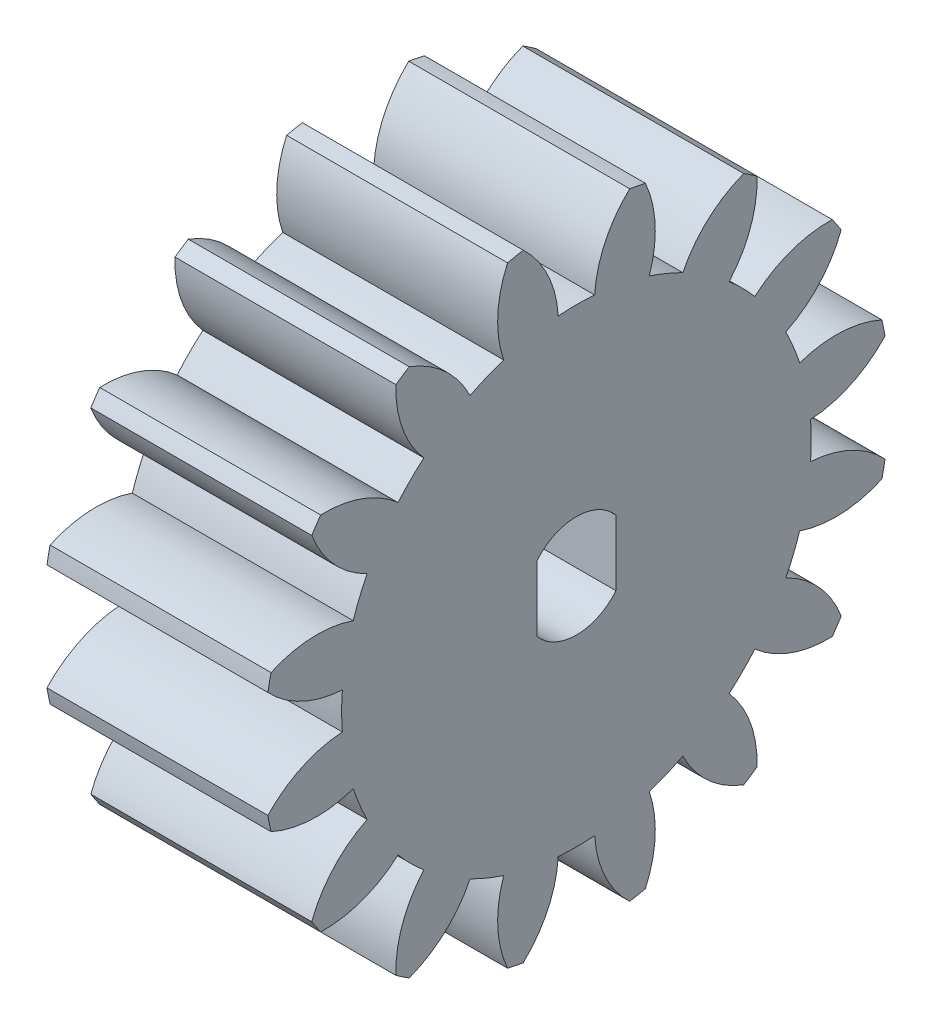
SolidWorks part; units mm, degrees
ref_plane "Plane1" through (0, 0, 0) normal (0, 0, 1) x (1, 0, 0)
ref_plane "Plane2" through (0, 0, 0) normal (0, 1, 0) x (1, 0, 0)
ref_plane "Plane3" through (0, 0, 0) normal (1, 0, 0) x (0, 0, -1)
sketch "HoldingSke" plane through (0, 0, 0) normal (0, 1, 0) x (1, 0, 0)
  line L0 (0, 0) -> (0.9613, -0.2756)
  line L1 (-15, 0) -> (100, 0) construction
  line L2 (0, 0) -> (-2.1039, 2.3779)
  line L3 (0, 0) -> (-11.863, 4.5341)
  line L4 (0, 0) -> (8.3015, 2.3804)
  line L5 (0, 0) -> (-46.8476, -17.4728)
  line L6 (0, 0) -> (-5.2639, -3.5516)
  line L7 (-2.1039, 2.3779) -> (8.6589, 51.2071)
  line L8 (-76.2, 54.61) -> (-76.1, 54.61)
  line L9 (-71.009, 38.7566) -> (-53.1078, 45.2721)
  line L10 (-76.2, 71.12) -> (104.1128, 71.12)
  line L11 (0, 0) -> (-6.35, 0)
  line L12 (-76.2, 101.6) -> (-76.162, 101.6)
  line L13 (24.9733, 27.94) -> (52.9518, 28.4284)
  line L14 (24.9733, 27.94) -> (24.9743, 27.94)
  line L15 (24.9733, 27.94) -> (100.4006, 29.5858)
  line L16 (-63.627, -1) -> (-12.827, -1)
  circle A0 centre (0, 0) radius 0.5
  circle A1 centre (0, 0) radius 6.749
  circle A2 centre (0, 0) radius 37.5
  circle A3 centre (0, 0) radius 0.5
  dimension "MHD" = 13.498
  dimension "Hub_dia" = 75
  dimension "Bore" = 1
  dimension "MBD" = 1
  dimension "Num_teeth" = 16
  dimension "Pitch_radius" = 180.3128
  dimension "Pitch" = 1
  dimension "Width" = 6.35
  dimension "Overall_len" = 50
  dimension "Show_teeth" = 16
  dimension "Thickness" = 6.35
  dimension "OAL" = 50.0013
  dimension "T_dim" = 0.1
  dimension "Ap" = 20
  dimension "H" = 19.05
  dimension "Backlash" = 0.038
  dimension "Addendum_fac" = 1
  dimension "Dedendum_fac" = 1.25
  dimension "Clearance_fac" = 0.25
  dimension "Dedendum_add" = 0.001
  dimension "Module" = 1
sketch "BasProSke" plane through (0, 0, 0) normal (0, 1, 0) x (1, 0, 0)
  line L0 (-10, 0) -> (60, 0) construction
  line L1 (0, 0) -> (0, 9)
  line L2 (0, 0) -> (6.35, 0)
  line L3 (6.35, 0) -> (6.35, 9)
  line L4 (6.35, 9) -> (0, 9)
  dimension "Diameter" = 18
  dimension "Thickness" = 6.35
revolve "Base-Revolve" add sketch "BasProSke" angle 360 about L0
sketch "TooCutSke" plane through (0, 0, 0) normal (1, 0, 0) x (0, 0, -1)
  line L1 (0, 0) -> (0, 107) construction
  line L2 (0, 0) -> (-0.8506, 7.9547) construction
  line L3 (0, 0) -> (-3.1089, 15.6293) construction
  line L4 (-0.8506, 7.9547) -> (-1.5544, 7.8146) construction
  arc A0 (0.5238, 6.7286) -> (-0.5238, 6.7286) centre (0, 0) ccw
  arc A1 (1.5534, 8.8907) -> (-1.5534, 8.8907) centre (0, 0) ccw
  circle A2 centre (0, 0) radius 8 construction
  circle A3 centre (0, 0) radius 7.5175 construction
  arc A4 (-0.5238, 6.7286) -> (-1.5534, 8.8907) centre (-3.7179, 6.5338) ccw
  arc A5 (1.5534, 8.8907) -> (0.5238, 6.7286) centre (3.7179, 6.5338) ccw
  dimension "Root_dia" = 13.498
  dimension "Overcut_dia" = 18.0508
  dimension "Pitch_dia" = 16
  dimension "Base_dia" = 15.0351
  dimension "Flank_rad" = 3.2
  dimension "Half_ang" = 11.25
  dimension "Half_CT" = 0.7176
extrude "ToothCut" cut sketch "TooCutSke" along normal through all
fillet "Breaks" [suppressed] radius 0.02
fillet "RootFillets" [suppressed] radius 0.251
pattern_circular "TeethCuts" count 16 every 22.5 about axis through (-10, 0, 0) along (1, 0, 0) of "ToothCut", "RootFillets", "Breaks"
sketch "HubNeaOneSke" plane through (0, 0, 0) normal (-1, 0, 0) x (0, 0, 1)
  circle A0 centre (0, 0) radius 6.749
  dimension "Diameter" = 13.498
extrude "HubNearOne" [suppressed] add sketch "HubNeaOneSke" along normal blind 43.6513
sketch "HubNeaBotSke" plane through (0, 0, 0) normal (-1, 0, 0) x (0, 0, 1)
  circle A0 centre (0, 0) radius 6.749
  dimension "Diameter" = 13.498
extrude "HubNearBoth" [suppressed] add sketch "HubNeaBotSke" along normal blind 21.8256
ref_plane "FarPln" through (6.35, 0, 0) normal (1, 0, 0) x (0, 0, -1)
sketch "HubFarSke" plane through (6.35, 0, 0) normal (1, 0, 0) x (0, 0, -1)
  circle A0 centre (0, 0) radius 6.749
  dimension "Diameter" = 13.498
extrude "HubFar" [suppressed] add sketch "HubFarSke" along normal blind 21.8256
sketch "BorSke" plane through (0, 0, 0) normal (1, 0, 0) x (0, 0, -1)
  circle A0 centre (0, 0) radius 0.5
  dimension "Diameter" = 1
extrude "Bore" cut sketch "BorSke" along normal mid plane 100.0025
sketch "KeySke" plane through (0, 0, 0) normal (1, 0, 0) x (0, 0, -1)
  line L0 (-0.05, 0) -> (-0.05, 0.6)
  line L1 (-0.05, 0.6) -> (0.05, 0.6)
  line L2 (0.05, 0.6) -> (0.05, 0)
  line L3 (0, 0) -> (0, 34) construction
  line L4 (-0.05, 0) -> (0.05, 0)
  dimension "Offset" = 0.6
  dimension "Width" = 0.1
extrude "Keyway" [suppressed] cut sketch "KeySke" along normal mid plane 100.0025
pattern_circular "Keyway2" [suppressed] count 2 every 90 about axis through (-10, 0, 0) along (1, 0, 0)
sketch "Sketch1" plane through (6.35, 0, 0) normal (1, 0, 0) x (0, 0, -1)
  line L0 (-1.1367, 0.94) -> (-1.1367, -0.94)
  line L1 (1.1367, 0.94) -> (1.1367, -0.94)
  circle A0 centre (0, 0) radius 1.475
  dimension "D1" = 2.95
  dimension "D2" = 1.88
extrude "Cut-Extrude1" cut sketch "Sketch1" against normal blind 10
equation "' \"Module@HoldingSke\" = 6.35"
equation "' \"Num_teeth@HoldingSke\" = 12"
equation "' \"Ap@HoldingSke\" =  20"
equation "' \"Width@HoldingSke\" = 0.5 * 25.4"
equation "' \"Hub_dia@HoldingSke\"= 1 * 25.4"
equation "' \"Overall_len@HoldingSke\" = 1.0 * 25.4"
equation "' \"Bore@HoldingSke\" = 0.75 * 25.4"
equation "' \"T_dim@HoldingSke\" = 0.1 * 25.4"
equation "' \"Width@KeySke\" = 0.25 * 25.4"
equation "' \"Show_teeth@HoldingSke\" = 13"
equation "' \"Backlash@HoldingSke\" = 0.009 * 25.4"
equation "' \"Addendum_fac@HoldingSke\" = 1.0"
equation "' \"Dedendum_fac@HoldingSke\" = 1.25"
equation "' \"Dedendum_add@HoldingSke\" = 0.00005 * 25.4"
equation "' \"Clearance_fac@HoldingSke\" = 0.25"
equation "\"Pitch@HoldingSke\" = 1 / \"Module@HoldingSke\""
equation "\"Overcut_dia@TooCutSke\" = (\"Num_teeth@HoldingSke\" + 2 * \"Addendum_fac@HoldingSke\") / \"Pitch@HoldingSke\" + 0.002 * 25.4"
equation "\"Pitch_dia@TooCutSke\" = \"Num_teeth@HoldingSke\" / \"Pitch@HoldingSke\""
equation "\"Base_dia@TooCutSke\" = \"Num_teeth@HoldingSke\" / \"Pitch@HoldingSke\" * cos((\"Ap@HoldingSke\"  * 3.14159265 / 180))"
equation "\"Root_dia@TooCutSke\" = (\"Num_teeth@HoldingSke\" + 2) / \"Pitch@HoldingSke\" - 2 * (\"Addendum_fac@HoldingSke\" + \"Dedendum_fac@HoldingSke\") / \"Pitch@HoldingSke\" - \"Dedendum_add@HoldingSke\" * 2"
equation "\"Half_ang@TooCutSke\" = 180 / \"Num_teeth@HoldingSke\""
equation "\"Half_CT@TooCutSke\" = \"Num_teeth@HoldingSke\" / \"Pitch@HoldingSke\" * sin((3.14159265 / 2 / \"Num_teeth@HoldingSke\")) / 2 - 7 * \"Backlash@HoldingSke\" / 4"
equation "\"Flank_rad@TooCutSke\" = \"Num_teeth@HoldingSke\" / \"Pitch@HoldingSke\" / 5"
equation "\"Radius@RootFillets\" = \"Clearance_fac@HoldingSke\" / \"Pitch@HoldingSke\" + \"Dedendum_add@HoldingSke\""
equation "\"Break_rad@Breaks\" = 0.02 / \"Pitch@HoldingSke\""
equation "\"Thickness@HoldingSke\" = \"Width@HoldingSke\""
equation "\"OAL@HoldingSke\" = \"Thickness@HoldingSke\""
equation "\"MHD@HoldingSke\" = (\"Num_teeth@HoldingSke\" + 2) / \"Pitch@HoldingSke\" - 2 * (\"Addendum_fac@HoldingSke\" + \"Dedendum_fac@HoldingSke\")  / \"Pitch@HoldingSke\" - \"Dedendum_add@HoldingSke\" * 2"
equation "\"MBD@HoldingSke\" = (\"Num_teeth@HoldingSke\" + 2) / \"Pitch@HoldingSke\" - 2 * (\"Addendum_fac@HoldingSke\" + \"Dedendum_fac@HoldingSke\")  / \"Pitch@HoldingSke\" - \"Dedendum_add@HoldingSke\" * 2 - 0.002 * 25.4"
equation "\"MHD@HoldingSke\" = ((sgn( \"MHD@HoldingSke\" - \"Hub_dia@HoldingSke\" )-1)*( \"MHD@HoldingSke\" - \"Hub_dia@HoldingSke\" ))/-2+ \"Hub_dia@HoldingSke\""
equation "\"MBD@HoldingSke\" = ((sgn( \"MBD@HoldingSke\" - \"Bore@HoldingSke\" )-1)*( \"MBD@HoldingSke\" - \"Bore@HoldingSke\" ))/-2+ \"Bore@HoldingSke\""
equation "\"OAL@HoldingSke\" = ((sgn( \"OAL@HoldingSke\" - \"Overall_len@HoldingSke\" )+1)*( \"OAL@HoldingSke\" - \"Overall_len@HoldingSke\" ))/2 + \"Overall_len@HoldingSke\" + 0.000002 * 25.4"
equation "\"Num_teeth@TeethCuts\" = int( \"Show_teeth@HoldingSke\" ) + 1"
equation "\"Num_teeth@TeethCuts\" = ((sgn( \"Num_teeth@TeethCuts\" - \"Num_teeth@HoldingSke\" )-1)*( \"Num_teeth@TeethCuts\" - \"Num_teeth@HoldingSke\" ))/-2+ \"Num_teeth@HoldingSke\""
equation "\"Num_teeth@TeethCuts\" = ((sgn( \"Num_teeth@TeethCuts\" - 2.0)+1)*( \"Num_teeth@TeethCuts\" - 2.0))/2 +2.0"
equation "\"Angle@TeethCuts\" = 360.0 / \"Num_teeth@HoldingSke\""
equation "\"Diameter@BasProSke\" = (\"Num_teeth@HoldingSke\" + 2 * \"Addendum_fac@HoldingSke\") / \"Pitch@HoldingSke\""
equation "\"Thickness@BasProSke\"  = \"Thickness@HoldingSke\""
equation "' \"Fillet_rad@BasProSke\" =  \"Thickness@HoldingSke\" * 0.05"
equation "\"MHD@HoldingSke\" = ((sgn( \"MHD@HoldingSke\" - \"Root_dia@TooCutSke\" )-1)*( \"MHD@HoldingSke\" - \"Root_dia@TooCutSke\" ))/-2+ \"Root_dia@TooCutSke\""
equation "\"Diameter@HubNeaOneSke\" = \"MHD@HoldingSke\""
equation "\"Length@HubNearOne\" = \"OAL@HoldingSke\" - \"Thickness@BasProSke\""
equation "\"Diameter@HubNeaBotSke\" = \"MHD@HoldingSke\""
equation "\"Length@HubNearBoth\" = ( \"OAL@HoldingSke\" - \"Thickness@BasProSke\" ) / 2.0"
equation "\"Thickness@FarPln\" = \"Thickness@BasProSke\""
equation "\"Diameter@HubFarSke\" = \"MHD@HoldingSke\""
equation "\"Length@HubFar\" = ( \"OAL@HoldingSke\" - \"Thickness@BasProSke\" ) / 2.0"
equation "\"Diameter@BorSke\" = \"MBD@HoldingSke\""
equation "\"D1@Bore\" = \"OAL@HoldingSke\" * 2.0"
equation "\"D1@Keyway\" = \"OAL@HoldingSke\" * 2.0"
equation "\"Offset@KeySke\" = \"T_dim@HoldingSke\" + \"MBD@HoldingSke\" / 2.0"
equation "\"D2@Sketch1\"=\"whitemotorcutoutlength\""
equation "\"CageLeftBottomEdge\"=22.11mm"
equation "\"CageLeftTopEdge\"=22.11mm"
equation "\"CageRightBottomEdge\"=21.63mm"
equation "\"CageRightTopEdge\"=21.63mm"
equation "\"CageHeight\"=86.04mm"
equation "\"CageLength\"=73.76mm"
equation "\"CageTopScrewClearance\"=10mm"
equation "\"CageBottomScrewClearance\"=25mm"
equation "\"CageLeftTopDepth\"= 11.65mm"
equation "\"CageLeftBottomDepth\"=11.11mm"
equation "\"CageLeftTopHeight\"=8.56175mm"
equation "\"CageLeftBottomHeight\"=16mm"
equation "\"CageRightTopDepth\"= 11.05mm"
equation "\"CageRightBottomDepth\"=10.58mm"
equation "\"CageRightTopHeight\"=9.6mm"
equation "\"CageRightBottomHeight\"=15.49mm"
equation "\"CageLeftTopChannelDepth\"=2.41908mm"
equation "\"CageLeftBottomChannelDepth\"=2.588mm"
equation "\"CageLeftChannelHeight\"=11.7mm"
equation "\"CageRightTopChannelDepth\"=2.32mm"
equation "\"CageRightBottomChannelDepth\"=2.318mm"
equation "\"CageRightChannelHeight\"=10mm"
equation "\"CageChanRelHeight\"=23.99mm"
equation "\"CageChanRelDepth\"=5.492mm"
equation "\"CageChamberRadius\"=16.261mm"
equation "\"CageScrewDiameter\"=4.8mm"
equation "\"CageSetScrewDiameter\"=3.5mm"
equation "\"CageAxleRadius\"=6.639mm"
equation "\"CageAxleKeyHeight\"=1.619mm"
equation "\"CageAxleKeyWidth\"=2.662mm"
equation "\"CageHoseWindowWidth\"=16.29mm"
equation "\"CageHoseWindowHeight\"=26.5mm"
equation "\"CageHoseWindow-Edge\"=8.89mm"
equation "\"CageScrew-VerticalEdge\"=5.0mm"
equation "\"CageScrew-HorizontalEdge\"=7.5mm"
equation "\"CageScrew-HoseCornerScrewEdge\"=4.45mm"
equation "\"CageAxle-BottomEdge\"=56.05mm"
equation "\"CageAxle-FrontEdge\"=46.03mm"
equation "\"CageBackSetScrew-Axle\"=40mm"
equation "\"CageFrontSetScrew-Axle\"=22mm"
equation "\"CageVelocityWindow-BackEdge\"=34.8mm"
equation "\"CageVelocityWindow-BottomEdge\"=27.55mm"
equation "\"CageVelocityWindowHeight\"=22.29mm"
equation "\"CageVelocityWindowWidth\"=12.61mm"
equation "\"TriggerSlot-BottomEdge\"=6.35mm"
equation "\"TriggerSlot-FrontEdge\"=15mm"
equation "\"TriggerSlotSize\"=6.7mm"
equation "\"TriggerRackOffset\"=.236224in"
equation "\"TriggerSlotSizeInt\"=.25in"
equation "\"MotorMountLegLength\"=.25in"
equation "\"GearOffset\"=.264907in"
equation "\"TriggerSlotSpacing\"=.25in"
equation "\"TriggerMiniSlotWidth\"=3.5mm"
equation "\"TriggerRackWidth\"=6.5mm"
equation "\"whitemotordepth\"=11.27mm"
equation "\"whitemotorbackdepth\"=3.845mm"
equation "\"whitemotoraxledepth\" = 3.5mm"
equation "\"whitemotoraxleoffset\"=11.4mm"
equation "\"whitemotorwidth\"=12.07mm"
equation "\"whitemotorheight\"=16.68mm"
equation "\"whitemotorcylinderlength\" =13.04mm"
equation "\"whitemotorcylinderradius\"=3.845mm"
equation "\"whitemotorcylinderoffset\"=2.35mm"
equation "\"whitemotorcutoutlength\"=1.88mm"
equation "\"whitemotorouterrad\"=5mm"
equation "\"whitemotorinnerrad\"=2.95mm"
equation "\"elasticracklength\"=2in"
equation "\"elasticrackpegsize\"=.25in"
equation "\"elasticrackpegbuffer\"=.125in"
equation "\"elasticrackpegspacing\"=1.76476378in"
equation "\"elasticbaybuffer\"=.25in"
equation "\"elasticdepth\"=.125in"
equation "\"elasticbaydepth\"=.75in"
equation "\"motormountwidth\"=12mm"
equation "\"motormountcornerfillet\"=3mm"
equation "\"D1@Sketch1\"=\"whitemotorinnerrad\""
equation "\"pandiscradius\"=14in"
equation "\"towermaterialwidth\"=.25in"
equation "\"towerslotlength\"=.5in"
equation "\"towermarkerspace\"=5in"
equation "\"towerslothorizoffset\"=1in"
equation "\"towerslothorizspacing\"=2in"
equation "\"towerslotvertoffset\"=3in"
equation "\"towerslotvertspacing\"=1in"
equation "\"towerheight\"=12in"
equation "\"towerupslot\"=1in"
equation "\"toweraxle\"=.5in"
equation "\"stepperouterrad\"=10mm"
equation "\"stepperscrewsize\"=3.45mm"
equation "\"stepperscrewc2c\"=49.5mm"
equation "\"stepperdepthoffset\"=24mm"
equation "\"stepperhorizoffset\"=22.91mm"
equation "\"shaftslotOD\"=18.8mm"
equation "\"shaftslotID\"=13.28mm"
equation "\"shaftkeywidth\"=2.67mm"
equation "\"shaftkeydepth\"=1.8mm"
equation "\"shaftcollartotaldepth\"=12.5mm"
equation "\"shaftsquaredepth\"=6mm"
equation "\"shaftsetscrewsize\"=3.5mm"
equation "\"shaftkeytightdepth\"=1.85mm"
equation "\"shaftslottightID\"=12.78mm"
equation "\"shaftsetscrewoffset\"=9mm"
equation "\"cagecollartotaldepth\"=10mm"
equation "\"cagecollartotalwidth\"=35mm"
equation "\"cagecollarbasedepth\"=4mm"
equation "\"gearhubintdiam\"=30mm"
equation "\"gearhubintwid\"=15mm"
equation "\"towerspeedwidth\"=2in"
equation "\"towerspeedheight\"=8in"
equation "\"towerspeedgap\"=2in"
equation "\"stepperaxleflat\"=.037in"
equation "\"stepperaxlerad\"=0.11811024in"
equation "\"ajaxaxlesize\"=3.87mm"
equation "\"ajaxinnercut\"=2.3mm"
equation "\"ajaxwidth\"=6.1mm"
equation "\"ajaxdiametral\"=25.8854"
equation "\"ajaxcutoutdepth\"=2.3mm"
equation "\"ajax4020gap\"=29.5mm"
equation "\"ajax4010gap\"=24.5mm"
equation "\"ajax20hubbuffer\"=0.240157in"
equation "\"ajax20hubholeoffset\"=.19685in"
equation "\"ajax20hubholesize\"=.059055in"
equation "\"ajax20cutoutint\"=13.4mm"
equation "\"ajax40hubholesize\"=7.21mm"
equation "\"ajax40hubholeoffset\"=10mm"
equation "\"ajax40hubbuffer\"=.350394in"
equation "\"ajax40cutoutint\"=32.6mm"
equation "\"bearingpandiscrad\"=6.8in"
equation "\"bearingpandiscang\"=48.75deg"
equation "\"bearingclearholedist\"=4.7345in"
equation "\"bearingclearholesize\"=.5in"
equation "\"bearingclearholeang\"=22.5deg"
equation "\"bearingmountholedist\"=4.25in"
equation "\"bearingwirehole\"=1.5in"
equation "\"no6diam\"=.146in"
equation "\"shortconangle\"=20deg"
equation "\"shortconlen\"=.875in"
equation "\"longconlen\"=1.25in"
equation "\"longconangle\"=15deg"
equation "\"TGMGearFaceDiameter\"=24.40mm"
equation "\"TGMCylinderLength\"=15.00mm"
equation "\"TGMScrewHole-Center\"=8.70mm"
equation "\"TGMScrewHoleDiameter\"=5.04mm"
equation "\"TGMCenterHoleDiameter\"=9.50mm"
equation "\"TGMShaftCollarSideLength\"=19.00mm"
equation "\"TGMShaftCollarDockingDepth\"=7.00mm"
equation "\"towerplatslotoffset\"=1.5in"
equation "\"towermotorpanelheight\"=10in"
equation "\"towerplatdepth\"=2in"
equation "\"ajaxhubdepth\"=.25in"
equation "\"shconangle\"=20deg"
equation "\"shconlen\"=1in"
equation "\"lnconlen\"=1.5in"
equation "\"lnconangle\"=15deg"
